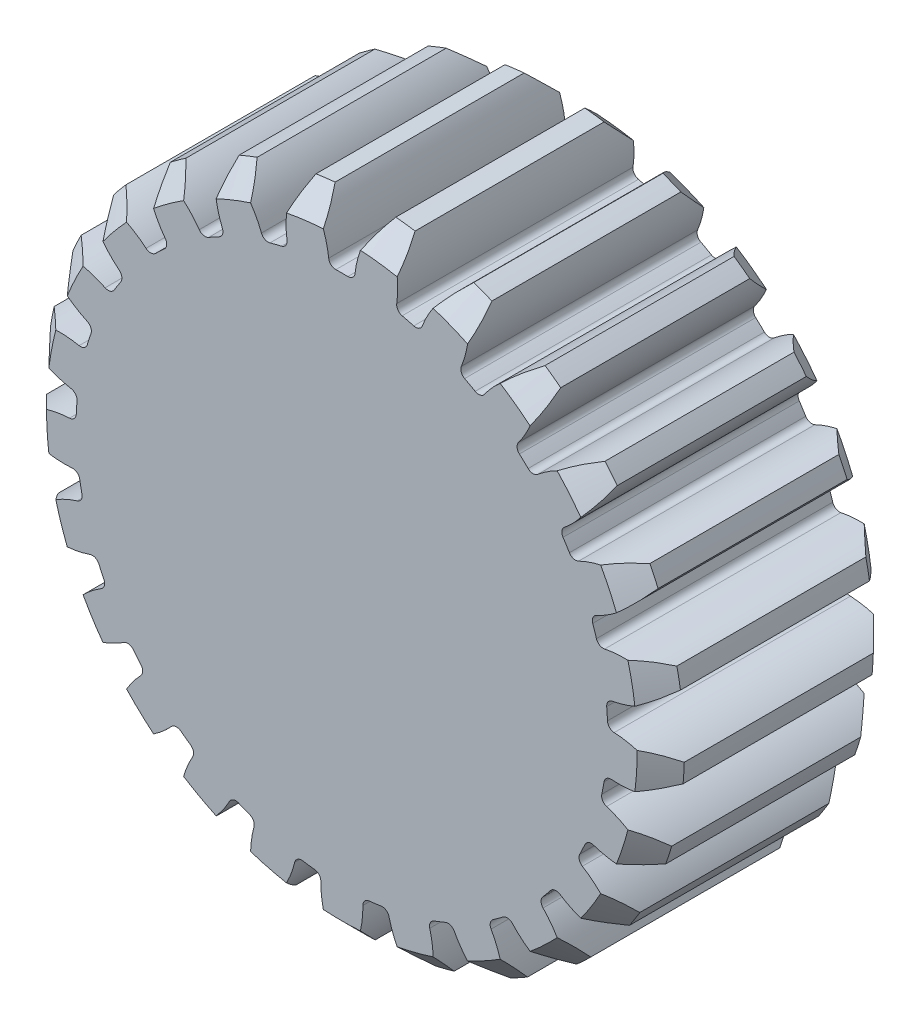
SolidWorks part; units mm, degrees
ref_plane "Front Plane" through (0, 0, 0) normal (0, 0, 1) x (1, 0, 0)
ref_plane "Top Plane" through (0, 0, 0) normal (0, 1, 0) x (1, 0, 0)
ref_plane "Right Plane" through (0, 0, 0) normal (1, 0, 0) x (0, 0, -1)
sketch "Sketch1" plane through (0, 0, 0) normal (0, 0, 1) x (1, 0, 0)
  circle A0 centre (0, 0) radius 25 construction
  circle A1 centre (0, 0) radius 27
  dimension "D1" = 50
  dimension "D2" = 54
extrude "Boss-Extrude1" add sketch "Sketch1" along normal mid plane 20
sketch "Sketch2" plane through (0, 0, 0) normal (0, 0, 1) x (1, 0, 0)
  line L0 (0, 0) -> (0, 27) construction
  line L1 (0, 0) -> (6.7146, 26.1517) construction
  line L2 (0, 0) -> (3.384, 26.7871) construction
  line L3 (-1.072, 22.4744) -> (0, 0) construction
  line L4 (-1.5698, 24.9507) -> (1.5698, 24.9507) construction
  line L5 (1.5698, 24.9507) -> (4.6845, 24.5572) construction
  line L6 (-2.2805, 26.9035) -> (0, 20.6378) construction
  circle A0 centre (0, 0) radius 23 construction
  circle A2 centre (0, 0) radius 27 construction
  arc A3 (-2.5691, 26.8775) -> (-1.072, 22.4744) centre (-9.4743, 22.0737) cw
  circle A4 centre (0, 0) radius 27 construction
  arc A5 (2.5691, 26.8775) -> (1.072, 22.4744) centre (9.4743, 22.0737) ccw
  circle A6 centre (0, 0) radius 25 construction
  arc A7 (1.072, 22.4744) -> (-1.072, 22.4744) centre (0, 0) ccw
  arc A8 (2.5691, 26.8775) -> (-2.5691, 26.8775) centre (0, 0) ccw
  dimension "D1" = 14.4
  dimension "D2" = 4
  dimension "D4" = 20
  dimension "D3" = 0.5
extrude "Cut-Extrude1" cut sketch "Sketch2" against normal through all both and the other way through all contours A5 A8 A3 A7
fillet "Fillet1" radius 0.6 2 edges at (1.072, 22.4744, 0) (-1.072, 22.4744, 0)
chamfer "Chamfer1" distance 2 angle 45 2 edges at (0, -27, -10) (0, -27, 10)
pattern_circular "CirPattern1" count 25 over 360 about axis through (0, 0, 0) along (0, 0, 1) of "Fillet1", "Cut-Extrude1"
equation "\"Module\"= 2"
equation "\"Number of Teeth\"= 25'Number of Teeth"
equation "\"Pressure Angle\"= 20"
equation "\"D1@Sketch1\"=\"Module\" * \"Number of Teeth\""
equation "\"D2@Sketch1\"=( \"Number of Teeth\" + 2) * \"Module\""
equation "\"D1@Sketch2\"=360 / \"Number of Teeth\""
equation "\"D2@Sketch2\"= \"Module\" * 2"
equation "\"D4@Sketch2\"=\"Pressure Angle\""
equation "\"D1@Fillet1\"=0.3 * \"Module\""
equation "\"D1@CirPattern1\"= \"Number of Teeth\""
equation "\"D1@Chamfer1\"= \"Module\""
